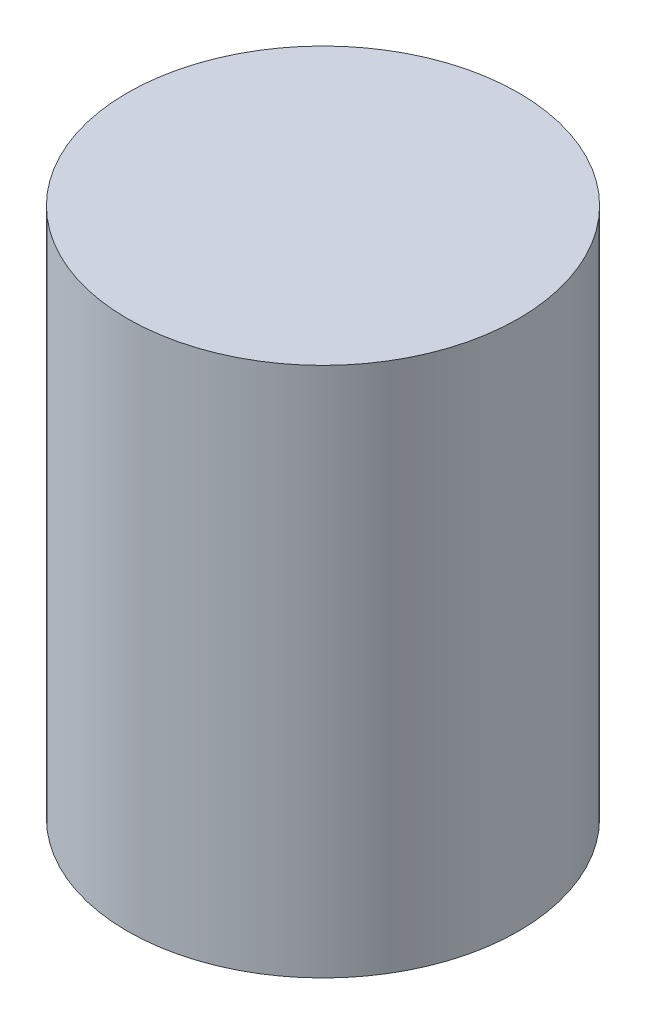
SolidWorks part; units mm, degrees
ref_plane "Front Plane" through (0, 0, 0) normal (0, 0, 1) x (1, 0, 0)
ref_plane "Top Plane" through (0, 0, 0) normal (0, 1, 0) x (1, 0, 0)
ref_plane "Right Plane" through (0, 0, 0) normal (1, 0, 0) x (0, 0, -1)
sketch "Sketch2" plane through (0, 0, 0) normal (0, 1, 0) x (1, 0, 0)
  circle A0 centre (0, 0) radius 7.89
  dimension "D1" = 15.78
extrude "Boss-Extrude1" add sketch "Sketch2" along normal blind 21.4
